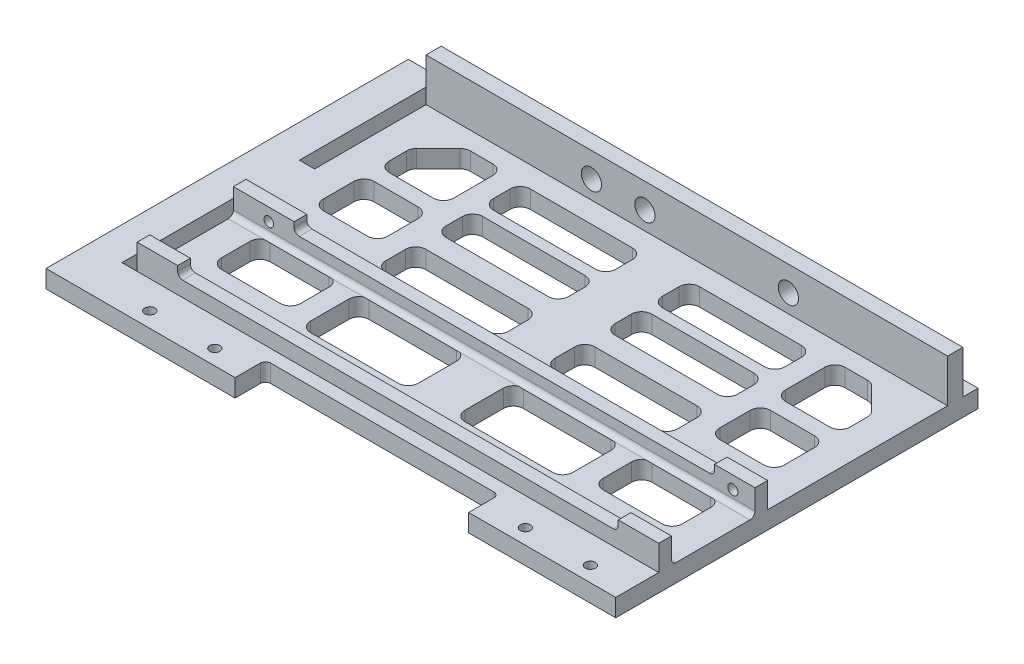
SolidWorks part; units mm, degrees
ref_plane "Front Plane" through (0, 0, 0) normal (0, 0, 1) x (1, 0, 0)
ref_plane "Top Plane" through (0, 0, 0) normal (0, 1, 0) x (1, 0, 0)
ref_plane "Right Plane" through (0, 0, 0) normal (1, 0, 0) x (0, 0, -1)
sketch "Sketch1" plane through (0, 0, 0) normal (0, 1, 0) x (1, 0, 0)
  line L1 (-51.5, -31.27) -> (51.5, -31.27)
  line L2 (-51.5, -31.27) -> (-51.5, 31.27)
  line L3 (-51.5, 31.27) -> (51.5, 31.27)
  line L4 (51.5, -31.27) -> (51.5, 31.27)
  line L5 (-51.5, -31.27) -> (51.5, 31.27) construction
  line L6 (-51.5, 31.27) -> (51.5, -31.27) construction
  point P0 (0, 0)
  dimension "D1" = 62.54
  dimension "D2" = 103
extrude "Boss-Extrude1" add sketch "Sketch1" along normal blind 3.5
sketch "Sketch2" plane through (0, 0, -31.27) normal (0, 0, -1) x (-1, 0, 0)
  line L4 (-51.5, 0) -> (51.5, 0)
  line L5 (51.5, 0) -> (51.5, 3.5)
  line L6 (51.5, 3.5) -> (-51.5, 3.5)
  line L7 (-51.5, 3.5) -> (-51.5, 0)
  line L8 (-51.5, 0) -> (51.5, 0)
  line L9 (51.5, 0) -> (51.5, 3.5)
  line L10 (51.5, 3.5) -> (-51.5, 3.5)
  line L11 (-51.5, 3.5) -> (-51.5, 0)
  dimension "D1" = 0
extrude "Boss-Extrude2" add sketch "Sketch2" along normal blind 3
sketch "Sketch5" plane through (0, 3.5, 0) normal (0, 1, 0) x (1, 0, 0)
  line L0 (51.5, 31.27) -> (43.5, 31.27)
  line L1 (51.5, -31.27) -> (51.5, 34.27) construction
  line L2 (43.5, 31.27) -> (43.5, 28.77)
  line L3 (43.5, 28.77) -> (51.5, 28.77)
  line L4 (51.5, 28.77) -> (51.5, 31.27)
  line L5 (0, -38.0579) -> (0, 51.3631) construction
  line L6 (-51.5, 34.27) -> (51.5, 34.27) construction
  dimension "D1" = 3
  dimension "D2" = 2.5
  dimension "D3" = 8
ref_plane "Plane1" through (0, 0, 0) normal (1, 0, 0) x (0, 0, -1)
sketch "Sketch8" plane through (0, 3.5, 0) normal (0, 1, 0) x (1, 0, 0)
  line L0 (51.5, -9.77) -> (-51.5, -9.77)
  line L3 (-51.5, -9.77) -> (-51.5, -7.27)
  line L4 (-51.5, -7.27) -> (51.5, -7.27)
  line L5 (51.5, -7.27) -> (51.5, -9.77)
  line L10 (-51.5, -31.27) -> (51.5, -31.27) construction
  dimension "D1" = 2.5
  dimension "D2" = 2.5
  dimension "D3" = 21.5
extrude "Boss-Extrude6" add sketch "Sketch8" along normal blind 3
sketch "Sketch9" plane through (0, 6.5, 0) normal (0, 1, 0) x (1, 0, 0)
  line L0 (51.5, -9.77) -> (43.5, -9.77)
  line L1 (-51.5, -9.77) -> (51.5, -9.77) construction
  line L2 (43.5, -9.77) -> (43.5, -7.27)
  line L3 (51.5, -7.27) -> (-51.5, -7.27) construction
  line L4 (43.5, -7.27) -> (51.5, -7.27)
  line L5 (51.5, -7.27) -> (51.5, -9.77)
  dimension "D1" = 8
extrude "Boss-Extrude7" add sketch "Sketch9" along normal blind 2
sketch "Sketch11" plane through (0, 0, 9.77) normal (0, 0, 1) x (1, 0, 0)
  line L0 (43.5, 8.5) -> (51.5, 8.5) construction
  line L1 (51.5, 8.5) -> (51.5, 3.5) construction
  circle A0 centre (47.13, 6) radius 1
  dimension "D1" = 2
  dimension "D2" = 4.37
  dimension "D3" = 2.5
extrude "Cut-Extrude3" cut sketch "Sketch11" against normal blind 22
fillet "Fillet4" radius 1 1 edges at (0, 3.5, 9.77)
sketch "Sketch12" plane through (0, 6.5, 0) normal (0, 1, 0) x (1, 0, 0)
  line L0 (-51.5, -9.77) -> (-39.5, -9.77)
  line L1 (-51.5, -9.77) -> (43.5, -9.77) construction
  line L2 (-39.5, -9.77) -> (-39.5, -7.27)
  line L3 (43.5, -7.27) -> (-51.5, -7.27) construction
  line L4 (-39.5, -7.27) -> (-51.5, -7.27)
  line L5 (-51.5, -7.27) -> (-51.5, -9.77)
  dimension "D1" = 12
extrude "Boss-Extrude8" add sketch "Sketch12" along normal blind 2
fillet "Fillet5" radius 1 1 edges at (-39.5, 6.5, 8.52)
sketch "Sketch13" plane through (0, 0, 9.77) normal (0, 0, 1) x (1, 0, 0)
  line L0 (-51.5, 8.5) -> (-51.5, 4.5) construction
  line L1 (-51.5, 8.5) -> (-39.5, 8.5) construction
  circle A0 centre (-44.5, 6) radius 0.9513
  dimension "D1" = 7
  dimension "D2" = 2.5
extrude "Cut-Extrude4" cut sketch "Sketch13" against normal blind 12
fillet "Fillet6" radius 1 1 edges at (43.5, 6.5, 8.52)
sketch "Sketch14" plane through (0, 3.5, 0) normal (0, 1, 0) x (1, 0, 0)
  line L0 (51.5, -28.77) -> (-51.5, -28.77)
  line L1 (-51.5, -28.77) -> (-51.5, -26.27)
  line L2 (-51.5, -10.77) -> (-51.5, -31.27) construction
  line L3 (-51.5, -26.27) -> (51.5, -26.27)
  line L4 (51.5, -31.27) -> (51.5, -10.77) construction
  line L5 (51.5, -26.27) -> (51.5, -28.77)
  line L6 (-51.5, -31.27) -> (51.5, -31.27) construction
  dimension "D1" = 2.5
  dimension "D2" = 2.5
extrude "Boss-Extrude9" add sketch "Sketch14" along normal blind 3
sketch "Sketch15" plane through (0, 6.5, 0) normal (0, 1, 0) x (1, 0, 0)
  line L0 (51.5, -28.77) -> (43.5, -28.77)
  line L1 (-51.5, -28.77) -> (51.5, -28.77) construction
  line L2 (43.5, -28.77) -> (43.5, -26.27)
  line L3 (51.5, -26.27) -> (-51.5, -26.27) construction
  line L4 (43.5, -26.27) -> (51.5, -26.27)
  line L5 (51.5, -26.27) -> (51.5, -28.77)
  line L6 (-51.5, -28.77) -> (-51.5, -26.27)
  line L7 (-51.5, -26.27) -> (-43.5, -26.27)
  line L8 (-43.5, -26.27) -> (-43.5, -28.77)
  line L9 (-43.5, -28.77) -> (-51.5, -28.77)
  dimension "D1" = 8
  dimension "D2" = 8
  dimension "D3" = 2.5
extrude "Boss-Extrude10" add sketch "Sketch15" along normal up to surface (2 mm away) up to face at (47.5, 8.5, 8.52)
sketch "Sketch16" plane through (0, 0, 31.27) normal (0, 0, 1) x (1, 0, 0)
  line L0 (43.5, 8.5) -> (51.5, 8.5) construction
  line L2 (51.5, 3.5) -> (51.5, 0) construction
  line L3 (-51.5, 3.5) -> (-51.5, 0) construction
  line L4 (-51.5, 8.5) -> (-43.5, 8.5) construction
  circle A0 centre (47.5, 4.5) radius 1
  circle A1 centre (-47.5, 4.5) radius 1
  dimension "D5" = 2
  dimension "D6" = 2
  dimension "D1" = 4
  dimension "D2" = 4
  dimension "D3" = 4
  dimension "D4" = 4
fillet "Fillet7" radius 1 3 edges at (0, 3.5, 26.27) (43.5, 6.5, 27.52) (-43.5, 6.5, 27.52)
sketch "Sketch17" plane through (0, 3.5, 0) normal (0, 1, 0) x (1, 0, 0)
  line L0 (43.5, -20.1173) -> (31.8853, -20.1173)
  line L1 (29.8853, -18.1173) -> (29.8853, -12.5081)
  line L2 (31.8853, -10.5081) -> (43.5, -10.5081)
  line L3 (45.5, -12.5081) -> (45.5, -18.1173)
  line L4 (25.8853, -20.1211) -> (25.8853, -12.5858)
  line L5 (23.8853, -10.5858) -> (6.6087, -10.5858)
  line L6 (4.6087, -12.5858) -> (4.6087, -20.1211)
  line L7 (6.6087, -22.1211) -> (23.8853, -22.1211)
  line L8 (44.9142, 19.849) -> (40.6192, 24.144)
  line L9 (39.205, 24.7298) -> (34.7808, 24.7298)
  line L10 (32.7808, 22.7298) -> (32.7808, 15.003)
  line L11 (34.7808, 13.003) -> (43.5, 13.003)
  line L12 (45.5, 15.003) -> (45.5, 18.4348)
  line L13 (43.5, 10.003) -> (34.7808, 10.003)
  line L14 (32.7808, 8.003) -> (32.7808, 2)
  line L15 (34.7808, 0) -> (43.5, 0)
  line L16 (45.5, 2) -> (45.5, 8.003)
  line L17 (28.7808, -2.3836) -> (28.7808, 1.5152)
  line L18 (26.7808, 3.5152) -> (6.6087, 3.5152)
  line L19 (4.6087, 1.5152) -> (4.6087, -2.3836)
  line L20 (6.6087, -4.3836) -> (26.7808, -4.3836)
  line L21 (28.7808, 9.5152) -> (28.7808, 12.74)
  line L22 (26.7808, 14.74) -> (6.6087, 14.74)
  line L23 (4.6087, 12.74) -> (4.6087, 9.5152)
  line L24 (6.6087, 7.5152) -> (26.7808, 7.5152)
  line L25 (51.5, -25.27) -> (51.5, -10.77) construction
  line L26 (51.5, -7.27) -> (51.5, 34.27) construction
  line L28 (26.7808, 16.8713) -> (6.6087, 16.8713)
  line L29 (28.7808, 18.8713) -> (28.7808, 22.144)
  line L30 (26.7808, 24.144) -> (6.6087, 24.144)
  line L31 (4.6087, 18.8713) -> (4.6087, 22.144)
  arc A0 (4.6087, -2.3836) -> (6.6087, -4.3836) centre (6.6087, -2.3836) ccw
  arc A1 (28.7808, -2.3836) -> (26.7808, -4.3836) centre (26.7808, -2.3836) cw
  arc A2 (28.7808, 1.5152) -> (26.7808, 3.5152) centre (26.7808, 1.5152) ccw
  arc A3 (6.6087, 3.5152) -> (4.6087, 1.5152) centre (6.6087, 1.5152) ccw
  arc A4 (4.6087, 9.5152) -> (6.6087, 7.5152) centre (6.6087, 9.5152) ccw
  arc A5 (6.6087, 14.74) -> (4.6087, 12.74) centre (6.6087, 12.74) ccw
  arc A6 (28.7808, 12.74) -> (26.7808, 14.74) centre (26.7808, 12.74) ccw
  arc A7 (28.7808, 9.5152) -> (26.7808, 7.5152) centre (26.7808, 9.5152) cw
  arc A8 (32.7808, 15.003) -> (34.7808, 13.003) centre (34.7808, 15.003) ccw
  arc A9 (34.7808, 24.7298) -> (32.7808, 22.7298) centre (34.7808, 22.7298) ccw
  arc A10 (40.6192, 24.144) -> (39.205, 24.7298) centre (39.205, 22.7298) ccw
  arc A11 (44.9142, 19.849) -> (45.5, 18.4348) centre (43.5, 18.4348) cw
  arc A12 (43.5, 13.003) -> (45.5, 15.003) centre (43.5, 15.003) ccw
  arc A13 (32.7808, 2) -> (34.7808, 0) centre (34.7808, 2) ccw
  arc A14 (34.7808, 10.003) -> (32.7808, 8.003) centre (34.7808, 8.003) ccw
  arc A15 (43.5, 10.003) -> (45.5, 8.003) centre (43.5, 8.003) cw
  arc A16 (43.5, 0) -> (45.5, 2) centre (43.5, 2) ccw
  arc A17 (4.6087, -20.1211) -> (6.6087, -22.1211) centre (6.6087, -20.1211) ccw
  arc A18 (6.6087, -10.5858) -> (4.6087, -12.5858) centre (6.6087, -12.5858) ccw
  arc A19 (25.8853, -12.5858) -> (23.8853, -10.5858) centre (23.8853, -12.5858) ccw
  arc A20 (25.8853, -20.1211) -> (23.8853, -22.1211) centre (23.8853, -20.1211) cw
  arc A21 (31.8853, -20.1173) -> (29.8853, -18.1173) centre (31.8853, -18.1173) cw
  arc A22 (29.8853, -12.5081) -> (31.8853, -10.5081) centre (31.8853, -12.5081) cw
  arc A23 (43.5, -10.5081) -> (45.5, -12.5081) centre (43.5, -12.5081) cw
  arc A24 (43.5, -20.1173) -> (45.5, -18.1173) centre (43.5, -18.1173) ccw
  arc A25 (6.6087, 24.144) -> (4.6087, 22.144) centre (6.6087, 22.144) ccw
  arc A26 (6.6087, 16.8713) -> (4.6087, 18.8713) centre (6.6087, 18.8713) cw
  arc A27 (26.7808, 16.8713) -> (28.7808, 18.8713) centre (26.7808, 18.8713) ccw
  arc A28 (28.7808, 22.144) -> (26.7808, 24.144) centre (26.7808, 22.144) ccw
  point P30 (29.8853, -15.3127)
  point P37 (28.7808, 3.5152)
  point P40 (4.6087, 3.5152)
  point P71 (4.6087, -10.5858)
  dimension "D9" = 2
  dimension "D10" = 2
  dimension "D1" = 6
  dimension "D2" = 6
  dimension "D3" = 6
  dimension "D4" = 4
  dimension "D5" = 4
  dimension "D6" = 4
  dimension "D7" = 4
  dimension "D8" = 3
extrude "Cut-Extrude6" cut sketch "Sketch17" against normal blind 5
mirror "Mirror4" about plane through (0, 0, 0) normal (1, 0, 0) of "Cut-Extrude6"
sketch "Sketch18" plane through (0, 3.5, 0) normal (0, 1, 0) x (1, 0, 0)
  line L0 (51.5, -7.27) -> (51.5, 34.27) construction
  line L1 (51.5, 31.27) -> (-51.5, 31.27)
  line L2 (51.5, 31.27) -> (51.5, 28.27)
  line L3 (51.5, 28.27) -> (-51.5, 28.27)
  line L4 (-51.5, 31.27) -> (-51.5, 28.27)
  line L5 (-51.5, 34.27) -> (-51.5, -7.27) construction
  line L7 (-51.5, 34.27) -> (51.5, 34.27) construction
  dimension "D1" = 3
  dimension "D2" = 3
extrude "Boss-Extrude11" add sketch "Sketch18" along normal blind 8.5
sketch "Sketch20" plane through (0, 0, 31.27) normal (0, 0, 1) x (1, 0, 0)
  line L0 (-51.5, 3.5) -> (-51.5, 0)
  line L1 (-51.5, 0) -> (-23.66, 0)
  line L2 (-51.5, 0) -> (51.5, 0) construction
  line L3 (-23.66, 0) -> (-23.66, 3.5)
  line L4 (-51.5, 3.5) -> (51.5, 3.5) construction
  line L5 (-23.66, 3.5) -> (-51.5, 3.5)
  line L7 (51.5, 0) -> (22.45, 0)
  line L8 (51.5, 0) -> (51.5, 3.5)
  line L9 (51.5, 3.5) -> (22.45, 3.5)
  line L10 (22.45, 0) -> (22.45, 3.5)
  dimension "D1" = 27.84
  dimension "D2" = 29.05
extrude "Boss-Extrude12" add sketch "Sketch20" along normal blind 6
fillet "Fillet8" radius 1 2 edges at (22.45, 1.75, 31.27) (-23.66, 1.75, 31.27)
sketch "Sketch21" plane through (0, 0, 0) normal (0, -1, 0) x (1, 0, 0)
  line L0 (-51.5, 37.27) -> (-23.66, 37.27) construction
  line L1 (-51.5, -34.27) -> (-51.5, 37.27) construction
  line L2 (-23.66, 37.27) -> (-23.66, 32.27) construction
  circle A0 centre (-43.5, 34.27) radius 1
  circle A1 centre (-30.66, 34.27) radius 1
  point P10 (-23.66, 34.77)
  dimension "D1" = 2
  dimension "D2" = 2
  dimension "D3" = 3
  dimension "D4" = 3
  dimension "D5" = 8
  dimension "D6" = 7
extrude "Cut-Extrude7" cut sketch "Sketch21" against normal blind 6
mirror "Mirror5" about plane through (0, 0, 0) normal (1, 0, 0) of "Cut-Extrude7"
sketch "Sketch22" plane through (51.5, 0, 0) normal (1, 0, 0) x (0, 0, -1)
  line L1 (-37.27, 0) -> (34.27, 0)
  line L2 (-37.27, 0) -> (-37.27, 3.5)
  line L3 (-37.27, 3.5) -> (34.27, 3.5)
  line L4 (34.27, 0) -> (34.27, 3.5)
sketch "Sketch24" plane through (-51.5, 0, 0) normal (-1, 0, 0) x (0, 0, 1)
  line L1 (37.27, 0) -> (-34.27, 0)
  line L2 (37.27, 0) -> (37.27, 3.5)
  line L3 (37.27, 3.5) -> (-34.27, 3.5)
  line L4 (-34.27, 0) -> (-34.27, 3.5)
extrude "Boss-Extrude14" add sketch "Sketch24" along normal blind 6.5
sketch "Sketch25" plane through (0, 3.5, 0) normal (0, 1, 0) x (1, 0, 0)
  line L0 (-51.5, -28.77) -> (-51.5, -25.27) construction
  line L1 (-54.5, 31.27) -> (-51.5, 31.27)
  line L2 (-54.5, 31.27) -> (-54.5, 6.27)
  line L3 (-54.5, -28.77) -> (-51.5, -28.77)
  line L4 (-51.5, 31.27) -> (-51.5, 6.27)
  line L5 (-54.5, 31.27) -> (-53.2508, 6.27) construction
  line L6 (-54.5, -28.77) -> (-53.2508, -3.77) construction
  line L7 (-58, -37.27) -> (-58, 34.27) construction
  line L8 (51.5, 31.27) -> (-51.5, 31.27) construction
  line L9 (-51.5, -28.77) -> (51.5, -28.77) construction
  line L10 (-51.5, 6.27) -> (-54.5, 6.27)
  line L11 (-54.5, -3.77) -> (-51.5, -3.77)
  line L12 (-51.5, -3.77) -> (-51.5, -28.77)
  line L13 (-52.7492, -3.77) -> (-51.5, -28.77) construction
  line L14 (-52.7492, 6.27) -> (-51.5, 31.27) construction
  line L15 (-54.5, -3.77) -> (-54.5, -28.77)
  point P0 (-53, 1.25)
  dimension "D1" = 0
  dimension "D2" = 3.5
  dimension "D3" = 25
  dimension "D4" = 25
extrude "Cut-Extrude9" cut sketch "Sketch25" against normal blind 10
sketch "Sketch26" plane through (0, 0, -28.27) normal (0, 0, 1) x (1, 0, 0)
  circle A3 centre (-18.84, 7.1) radius 2
  circle A4 centre (-8.27, 7.1) radius 2
  circle A5 centre (20.06, 7.1) radius 2
  point P5 (0, 0)
extrude "Cut-Extrude10" cut sketch "Sketch26" against normal blind 10
sketch "Sketch27" plane through (-58, 0, 0) normal (-1, 0, 0) x (0, 0, 1)
  line L4 (37.27, 0) -> (37.27, 3.5)
  line L5 (37.27, 3.5) -> (-34.27, 3.5)
  line L6 (-34.27, 3.5) -> (-34.27, 0)
  line L7 (-34.27, 0) -> (37.27, 0)
  line L8 (37.27, 0) -> (37.27, 3.5)
  line L9 (37.27, 3.5) -> (-34.27, 3.5)
  line L10 (-34.27, 3.5) -> (-34.27, 0)
  line L11 (-34.27, 0) -> (37.27, 0)
  dimension "D1" = 0
extrude "Boss-Extrude15" add sketch "Sketch27" along normal blind 3
